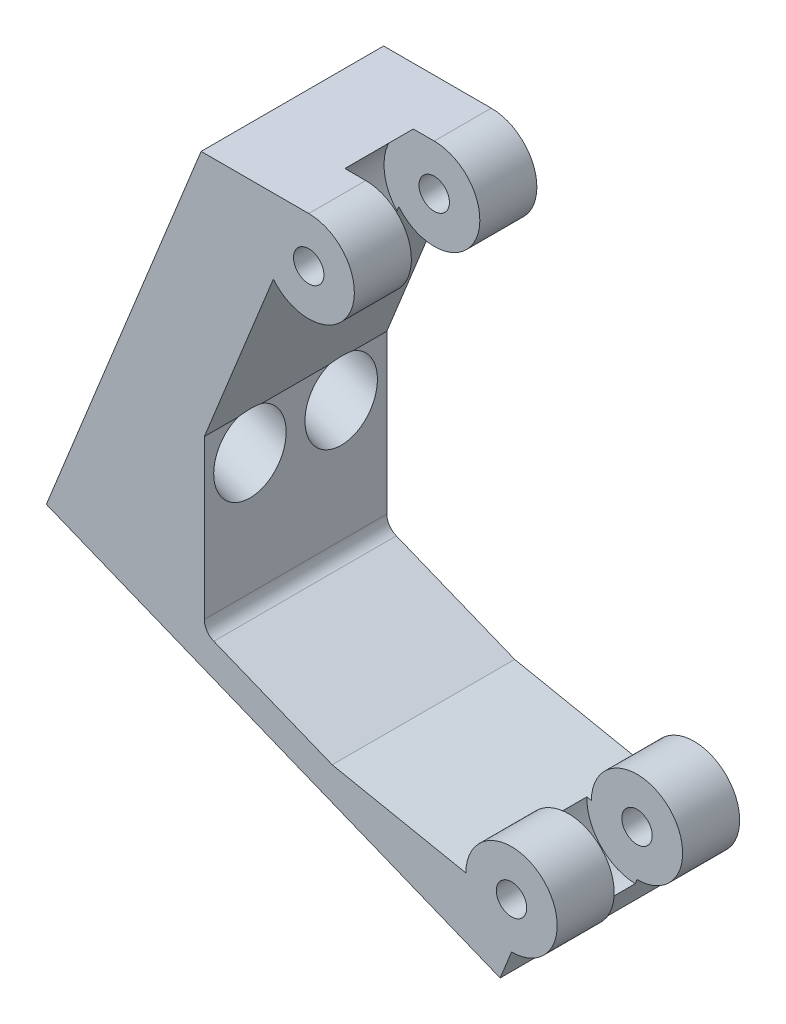
SolidWorks part; units mm, degrees
other "Markup1"
sketch "Sketch3" plane through (0, 0, 12) normal (0, 0, 1) x (1, 0, 0)
other "DetailItem1"
other "DetailItem3"
other "DetailItem5"
ref_plane "Front Plane" through (0, 0, 0) normal (0, 0, 1) x (1, 0, 0)
ref_plane "Top Plane" through (0, 0, 0) normal (0, 1, 0) x (1, 0, 0)
ref_plane "Right Plane" through (0, 0, 0) normal (1, 0, 0) x (0, 0, -1)
sketch "Sketch1" plane through (0, 0, 0) normal (0, 0, 1) x (1, 0, 0)
  line L2 (0, 6.6407) -> (0, 35.2105)
  line L3 (0, 35.2105) -> (8.8654, 35.2105)
  line L5 (6.5411, 30.3139) -> (2, 19.0743)
  line L6 (2, 19.0743) -> (2, 7.9897)
  line L7 (10.4069, 4.5931) -> (19.1992, 2.8287)
  line L11 (8.8654, 32.2105) -> (22.1992, 2.8287) construction
  line L15 (8.8654, 32.2105) -> (8.8654, 4.9405) construction
  line L16 (8.8654, 4.9405) -> (22.1992, 2.8287) construction
  line L17 (8.8654, 4.9405) -> (8.8654, -11.9834) construction
  line L21 (2, 7.9897) -> (10.4069, 4.5931)
  line L22 (-988.4786, -0.1713) -> (16.8603, -0.1713) construction
  line L23 (0, 6.6407) -> (21.45, -2.0257)
  line L24 (-905.7338, 372.5809) -> (46380.6427, -18732.3554) construction
  line L25 (22.1992, -0.1713) -> (50022.1992, -0.1713) construction
  line L26 (22.1992, -0.1713) -> (21.45, -2.0257)
  line L27 (-904.9846, 374.4353) -> (46381.392, -18730.501) construction
  line L28 (0.4221, 6.4701) -> (-46358.7706, 18736.7998) construction
  line L29 (2, 19.0743) -> (18732.3297, 46378.267) construction
  arc A0 (22.1992, -0.1713) -> (19.1992, 2.8287) centre (22.1992, 2.8287) ccw
  arc A1 (8.8654, 35.2105) -> (6.5411, 30.3139) centre (8.8654, 32.2105) cw
  circle A2 centre (8.8654, 32.2105) radius 1
  circle A3 centre (22.1992, 2.8287) radius 1
  dimension "D1" = 2
  dimension "D3" = 3
  dimension "D4" = 27.27
  dimension "D5" = 13.5
  dimension "D8" = 81
  dimension "D12" = 22
  dimension "D2" = 2
  dimension "D9" = 90
  dimension "D13" = 2
extrude "Boss-Extrude1" add sketch "Sketch1" along normal blind 12
ref_plane "midplane" through (0, 0, 6) normal (0, 0, 1) x (1, 0, 0)
sketch "Sketch2" plane through (0, 0, 6) normal (0, 0, 1) x (1, 0, 0)
  circle A0 centre (8.8654, 32.2105) radius 3.3
  circle A1 centre (22.1992, 2.8287) radius 3.3
  dimension "D1" = 6.6
extrude "Cut-Extrude1" cut sketch "Sketch2" against normal blind 2.25 and the other way blind 2.25
fillet "Fillet3" radius 1 1 edges at (2, 7.9897, 6)
ref_plane "Plane - base" through (-12.2296, 4.9411, 0) normal (-0.9272, 0.3746, 0) x (0, 0, -1)
sketch "Sketch4" plane through (-12.2296, 4.9411, 0) normal (-0.9272, 0.3746, 0) x (0, 0, -1)
  line L1 (-12, -32.6466) -> (0, -32.6466)
  line L2 (-12, -32.6466) -> (-12, -6.1571)
  line L3 (-12, -6.1571) -> (0, -6.1571)
  line L4 (0, -32.6466) -> (0, -6.1571)
extrude "Boss-Extrude2" add sketch "Sketch4" against normal up to surface up to face at (0, 20.9256, 6)
sketch "Hole sketch" plane through (7.6836, 33.1417, 0) normal (-0.9272, 0.3746, 0) x (0, 0, -1)
  line L0 (-12, 17.4202) -> (0, 17.4202) construction
  line L1 (-8.25, 3.3877) -> (-3.75, 3.3877) construction
  line L2 (0, 24.8243) -> (0, 15.1722) construction
  line L3 (-6, -1.7766) -> (-6, 49998.2234) construction
  line L4 (-6, 47.4664) -> (-6, 19.7472) construction
  line L5 (-12, 19.6681) -> (-12, 15.1722) construction
  line L6 (-12, 3.4206) -> (-12, 10.3547) construction
  line L7 (-12, 6.8877) -> (-6, 6.8877) construction
  circle A0 centre (-9, 17.4202) radius 1.2884
  circle A1 centre (-3, 17.4202) radius 1.2884
  circle A2 centre (-6, 6.8877) radius 1.2884
  point P8 (-9, 17.4202)
  point P9 (-3, 17.4202)
  point P10 (-6, 6.8877)
  dimension "D2" = 2.5768
  dimension "D1" = 3
  dimension "D3" = 3.5
extrude "Screw shaft holes" cut sketch "Hole sketch" against normal through all both and the other way through all
sketch "Sketch5" plane through (-4.9057, 1.982, 0) normal (0.9272, -0.3746, 0) x (0, 0, -1)
  circle A0 centre (-6, 26.7191) radius 2.3813
  circle A1 centre (-9, 16.1866) radius 2.3813
  circle A2 centre (-3, 16.1866) radius 2.3813
  dimension "D1" = 4.7625
extrude "Screw counterbores" cut sketch "Sketch5" against normal blind 2.5918 and the other way blind 5
sketch "Sketch6" plane through (-12.2296, 4.9411, 0) normal (-0.9272, 0.3746, 0) x (0, 0, 1)
  line L1 (-3.4001, 37.7488) -> (15.3252, 37.7488)
  line L2 (-3.4001, 37.7488) -> (-3.4001, 2.6951)
  line L3 (-3.4001, 2.6951) -> (15.3252, 2.6951)
  line L4 (15.3252, 37.7488) -> (15.3252, 2.6951)
extrude "Cut-Extrude2" cut sketch "Sketch6" against normal blind 1.66
equation "\"axle-diameter\"=2"
equation "\"D1@Sketch1\"=\"axle-diameter\""
equation "\"switch-thickness\"=12"
equation "\"D1@Boss-Extrude1\"=\"switch-thickness\""
equation "\"base-width\"=4.0"
equation "\"axle-bushing-radius\"=3"
equation "\"D3@Sketch1\"= \"axle-bushing-radius\""
equation "\"D1@Sketch2\"=\"axle-bushing-radius\"*2.2"
equation "\"D1@Cut-Extrude1\"=\"switch-thickness\"/6+\"clearance\""
equation "\"D2@Cut-Extrude1\"=\"switch-thickness\"/6+\"clearance\""
equation "\"clearance\"= 0.25"
equation "\"arm-width\"=3.0"
equation "\"min-diameter\"=70"
